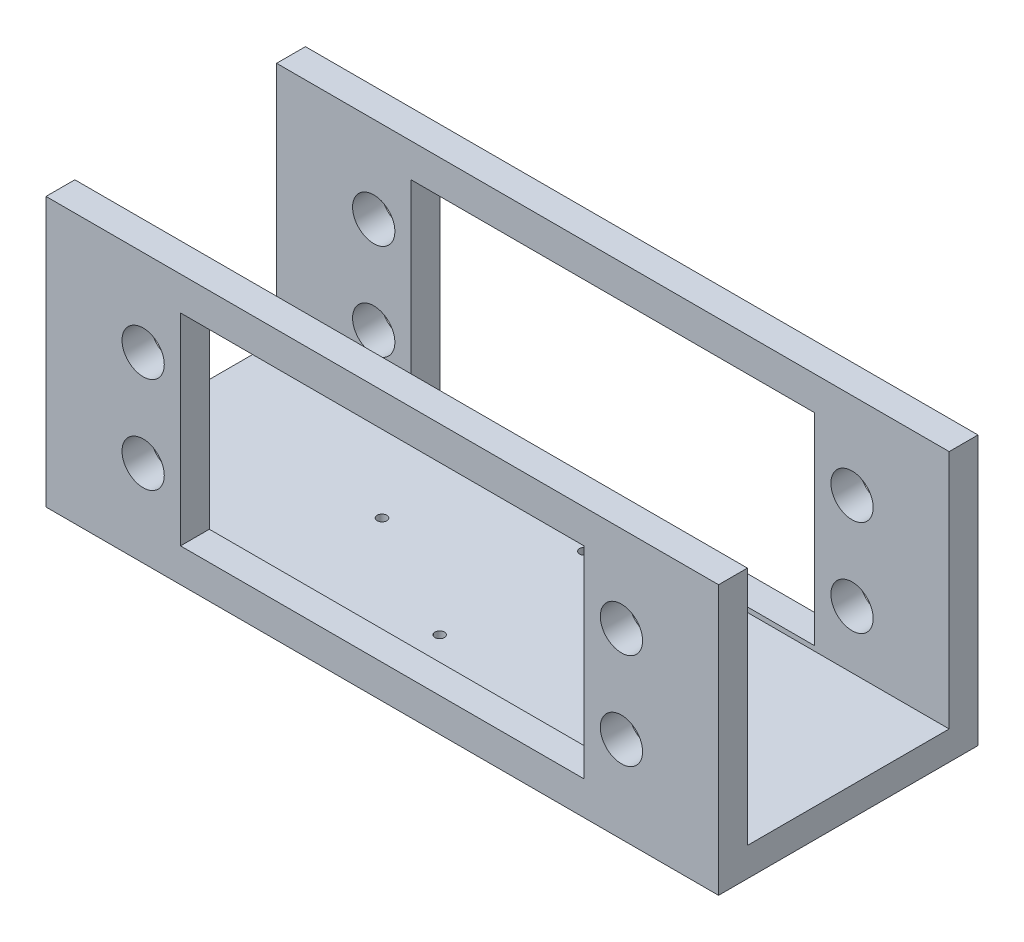
SolidWorks part; units mm, degrees
ref_plane "Front Plane" through (0, 0, 0) normal (0, 0, 1) x (1, 0, 0)
ref_plane "Top Plane" through (0, 0, 0) normal (0, 1, 0) x (1, 0, 0)
ref_plane "Right Plane" through (0, 0, 0) normal (1, 0, 0) x (0, 0, -1)
sketch "Sketch1" plane through (0, 0, 0) normal (0, 1, 0) x (1, 0, 0)
  line L0 (-35, 0) -> (35, 0) construction
  line L1 (-35, 13.5) -> (35, 13.5)
  line L2 (-35, 13.5) -> (-35, -13.5)
  line L3 (-35, -13.5) -> (35, -13.5)
  line L4 (35, 13.5) -> (35, -13.5)
  line L5 (-35, 13.5) -> (35, -13.5) construction
  line L6 (-35, -13.5) -> (35, 13.5) construction
  line L7 (0, 13.5) -> (0, -11.5802) construction
  circle A0 centre (-13.53, 0) radius 0.5
  circle A1 centre (0, 7.53) radius 0.5
  circle A2 centre (0, -7.53) radius 0.5
  circle A3 centre (13.53, 0) radius 0.5
  point P0 (0, 0)
  dimension "D4" = 1
  dimension "D6" = 1
  dimension "D1" = 27
  dimension "D2" = 70
  dimension "D3" = 13.53
  dimension "D5" = 7.53
extrude "Boss-Extrude2" add sketch "Sketch1" along normal blind 3
sketch "Sketch2" plane through (0, 3, 0) normal (0, 1, 0) x (1, 0, 0)
  line L0 (-35, -10.5) -> (35, -10.5)
  line L4 (35, -13.5) -> (35, 13.5)
  line L5 (35, 13.5) -> (-35, 13.5)
  line L6 (-35, 13.5) -> (-35, -13.5)
  line L7 (-35, -13.5) -> (35, -13.5)
  line L8 (35, -13.5) -> (35, 13.5)
  line L9 (35, 13.5) -> (-35, 13.5)
  line L10 (-35, 13.5) -> (-35, -13.5)
  line L11 (-35, -13.5) -> (35, -13.5)
  line M8 (35, -13.5) -> (35, 13.5)
  line M10 (-35, 13.5) -> (-35, -13.5)
  line M11 (-35, -13.5) -> (35, -13.5)
  dimension "D2" = 3
  dimension "D1" = 0
extrude "Boss-Extrude3" add sketch "Sketch2" along normal blind 25 contours L0 M10 M11 M8
sketch "Sketch3" plane through (0, 0, 13.5) normal (0, 0, 1) x (1, 0, 0)
  line L0 (0, 28) -> (0, 0) construction
  line L1 (-35, 14) -> (35, 14) construction
  line L3 (-21, 24.5) -> (21, 24.5)
  line L4 (-35, 0) -> (35, 0)
  line L5 (35, 0) -> (35, 28)
  line L6 (35, 28) -> (-35, 28)
  line L7 (-35, 28) -> (-35, 0)
  line L8 (-35, 0) -> (35, 0)
  line L9 (35, 0) -> (35, 28)
  line L10 (35, 28) -> (-35, 28)
  line L11 (-35, 28) -> (-35, 0)
  line L12 (-21, 24.5) -> (-21, 3.5)
  line L13 (-21, 3.5) -> (21, 3.5)
  line L14 (21, 24.5) -> (21, 3.5)
  line L15 (-21, 24.5) -> (21, 3.5) construction
  line L16 (-21, 3.5) -> (21, 24.5) construction
  circle A0 centre (-24.89, 19) radius 2.2
  circle A1 centre (-24.89, 9) radius 2.2
  circle A2 centre (24.89, 9) radius 2.2
  circle A3 centre (24.89, 19) radius 2.2
  point P8 (0, 14)
  dimension "D5" = 4.4
  dimension "D2" = 42
  dimension "D3" = 21
  dimension "D4" = 5
  dimension "D6" = 3.89
  dimension "D1" = 0
extrude "Cut-Extrude1" cut sketch "Sketch3" against normal blind 25 contours A1 | A0 | L12 L3 L14 L13 | A3 | A2
ref_plane "Plane2" through (0, 0, 0) normal (0, 0, 1) x (1, 0, 0)
mirror "Mirror1" about plane through (0, 0, 0) normal (0, 0, 1) of bodies 104
